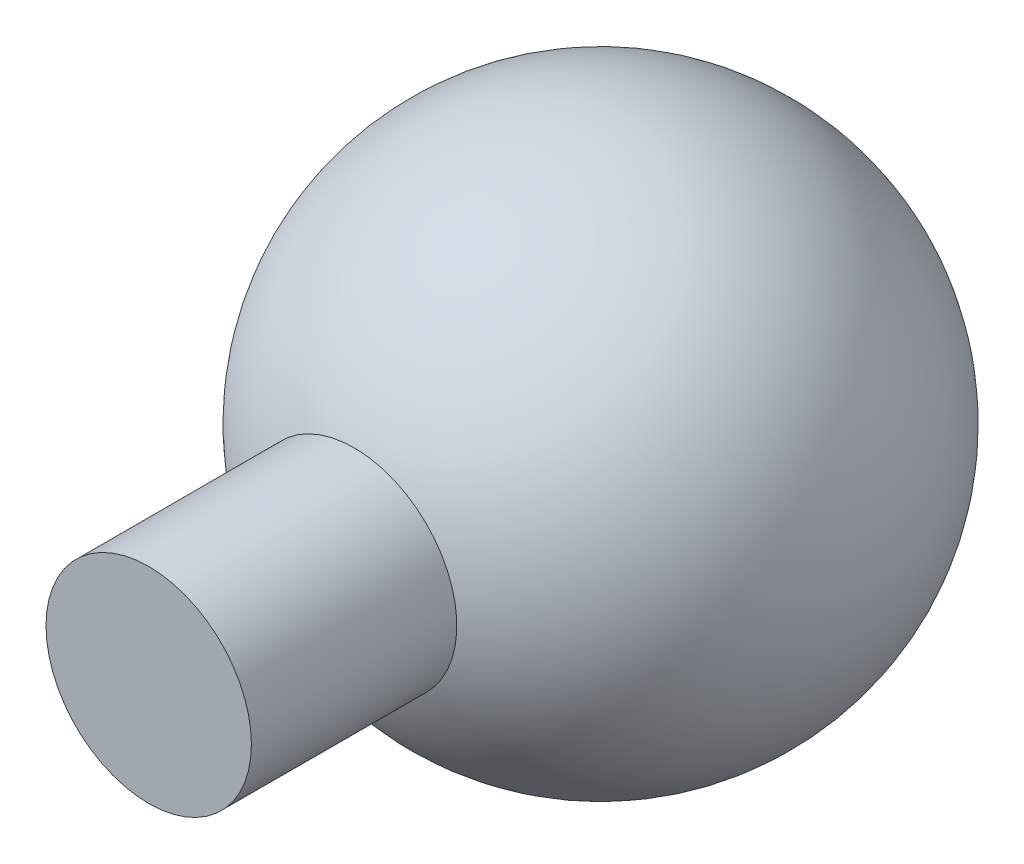
SolidWorks part; units mm, degrees
ref_plane "Front Plane" through (0, 0, 0) normal (0, 0, 1) x (1, 0, 0)
ref_plane "Top Plane" through (0, 0, 0) normal (0, 1, 0) x (1, 0, 0)
ref_plane "Right Plane" through (0, 0, 0) normal (1, 0, 0) x (0, 0, -1)
sketch "Sketch1" plane through (0, 0, 0) normal (0, 0, 1) x (1, 0, 0)
  line L0 (0, 11.8208) -> (0, -13.7909) construction
  line L1 (-13.9518, 0) -> (14.7157, 0) construction
  line L2 (0, 6.5) -> (0, -6.5)
  arc A0 (0, -6.5) -> (0, 6.5) centre (0, 0) ccw
  dimension "D1" = 13
revolve "Revolve1" add sketch "Sketch1" angle 360 about L0
sketch "Sketch2" plane through (0, 0, 0) normal (0, 0, 1) x (1, 0, 0)
  circle A0 centre (0, 0) radius 2.5
  dimension "D1" = 5
extrude "Boss-Extrude1" add sketch "Sketch2" along normal blind 11
